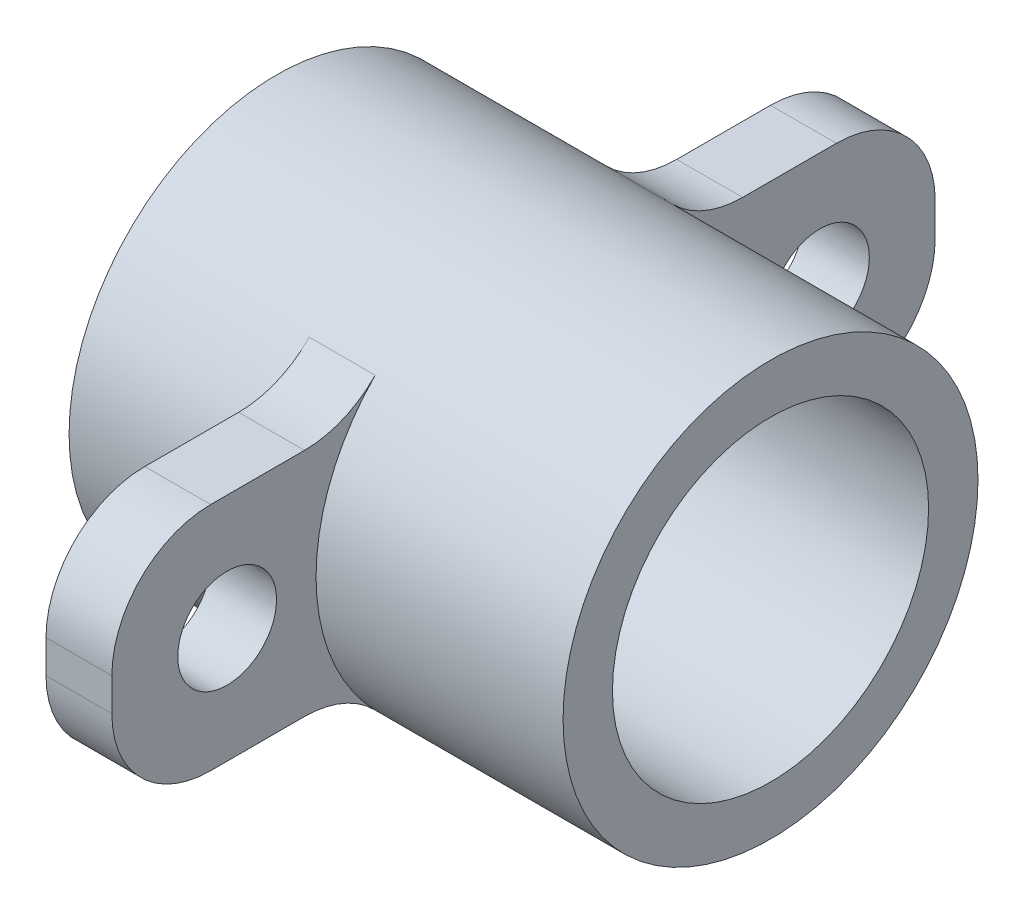
SolidWorks part; units mm, degrees
ref_plane "Front Plane" through (0, 0, 0) normal (0, 0, 1) x (1, 0, 0)
ref_plane "Top Plane" through (0, 0, 0) normal (0, 1, 0) x (1, 0, 0)
ref_plane "Right Plane" through (0, 0, 0) normal (1, 0, 0) x (0, 0, -1)
sketch "Sketch1" plane through (0, 0, 0) normal (1, 0, 0) x (0, 0, -1)
  circle A0 centre (0, 0) radius 6.3
  dimension "D1" = 12.6
extrude "Boss-Extrude1" add sketch "Sketch1" along normal mid plane 15
thread "Thread1" pitch 2 start angle 0, offset 1.8, length 0, pitch 2, diameter 14.6
ref_plane "Plane1" through (9.3, 0, 7.3) normal (0, -1, 0) x (0, 0, 1)
sketch "Thread Profile1" plane through (9.3, 0, 7.3) normal (0, -1, 0) x (0, 0, 1)
  line L0 (0, 0) -> (0, 2) construction
  line L11 (0, 0) -> (0, 1.75)
  line L12 (0, 1.75) -> (-1.0825, 1.125)
  line L13 (-1.0825, 1.125) -> (-1.0825, 0.625)
  line L15 (-1.0825, 0.625) -> (0, 0)
  line L17 (-1.0825, 0.875) -> (0, 0.875) construction
  point P2 (0, 0)
  dimension "Pitch" = 2
  dimension "Profile_Angle" = 60
  dimension "Profile_Land" = 0.5
  dimension "Profile_Height" = 1.0825
sketch "Sketch26" plane through (0, 0, 0) normal (1, 0, 0) x (0, 0, -1)
  line L0 (5.2383, 3.5) -> (12.5, 3.5)
  line L1 (12.5, 3.5) -> (12.5, -3.5)
  line L2 (12.5, -3.5) -> (5.2383, -3.5)
  line L3 (-9, 0) -> (9, 0) construction
  line L4 (-5.2383, -3.5) -> (-12.5, -3.5)
  line L5 (-12.5, -3.5) -> (-12.5, 3.5)
  line L6 (-12.5, 3.5) -> (-5.2383, 3.5)
  circle A1 centre (0, 0) radius 6.3 construction
  circle A2 centre (9, 0) radius 1.5
  circle A3 centre (-9, 0) radius 1.5
  arc A4 (-5.2383, 3.5) -> (-5.2383, -3.5) centre (0, 0) ccw
  arc A5 (5.2383, -3.5) -> (5.2383, 3.5) centre (0, 0) ccw
  point P20 (0, 0)
  dimension "D1" = 3
  dimension "D3" = 9
  dimension "D2" = 25
  dimension "D4" = 7
extrude "Boss-Extrude3" add sketch "Sketch26" against normal blind 2
fillet "Fillet1" radius 3 8 edges at (-1, 3.5, 5.2383) (-1, 3.5, 12.5) (-1, -3.5, 12.5) (-1, -3.5, 5.2383) (-1, -3.5, -5.2383) (-1, -3.5, -12.5) (-1, 3.5, -12.5) (-1, 3.5, -5.2383)
sketch "Sketch24" plane through (-7.5, 0, 0) normal (-1, 0, 0) x (0, 0, 1)
  circle A0 centre (0, 0) radius 4.8
  dimension "D1" = 9.6
extrude "Cut-Extrude1" cut sketch "Sketch24" against normal through all
